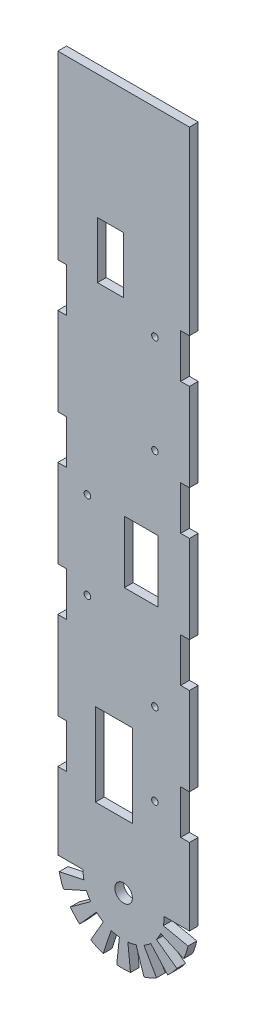
SolidWorks part; units mm, degrees
ref_plane "Front Plane" through (0, 0, 0) normal (0, 0, 1) x (1, 0, 0)
ref_plane "Top Plane" through (0, 0, 0) normal (0, 1, 0) x (1, 0, 0)
ref_plane "Right Plane" through (0, 0, 0) normal (1, 0, 0) x (0, 0, -1)
sketch "Sketch1" plane through (0, 0, 0) normal (0, 0, 1) x (1, 0, 0)
  line L0 (-30, 34.9376) -> (-30, 0)
  line L1 (0, 317.2805) -> (0, 289.6261) construction
  line L2 (30, 317.2805) -> (30, 234.9376)
  line L3 (30, 317.2805) -> (-30, 317.2805)
  line L4 (0, 270.6261) -> (0, 0) construction
  line L5 (-30, 317.2805) -> (30, 317.2805)
  line L6 (18.5, 0) -> (30, 0)
  line L7 (-11.9247, 260.6261) -> (0, 260.6261)
  line L8 (-11.9247, 260.6261) -> (-11.9247, 234.9355)
  line L9 (-11.9247, 234.9355) -> (0, 234.9355)
  line L10 (0, 260.6261) -> (0, 234.9355)
  line L11 (15.5956, 120.6731) -> (0.3306, 120.6731)
  line L12 (15.5956, 120.6731) -> (15.5956, 148.8989)
  line L13 (15.5956, 148.8989) -> (0.3306, 148.8989)
  line L14 (30, 234.9376) -> (26, 234.9355)
  line L15 (26, 234.9355) -> (26, 214.9355)
  line L16 (26, 214.9355) -> (30, 214.9376)
  line L17 (30, 214.9376) -> (30, 174.9376)
  line L18 (26, 174.9355) -> (30, 174.9376)
  line L19 (26, 174.9355) -> (26, 154.9355)
  line L20 (26, 154.9355) -> (30, 154.9376)
  line L21 (30, 154.9376) -> (30, 114.9376)
  line L22 (26, 114.9355) -> (30, 114.9376)
  line L23 (26, 114.9355) -> (26, 94.9355)
  line L24 (26, 94.9355) -> (30, 94.9376)
  line L25 (30, 94.9376) -> (30, 54.9376)
  line L26 (26, 54.9355) -> (30, 54.9376)
  line L27 (26, 54.9355) -> (26, 34.9355)
  line L28 (26, 34.9355) -> (30, 34.9376)
  line L29 (30, 34.9376) -> (30, 0)
  line L30 (-26, 34.9355) -> (-30, 34.9376)
  line L31 (-26, 54.9355) -> (-26, 34.9355)
  line L32 (-26, 54.9355) -> (-30, 54.9376)
  line L33 (-30, 94.9376) -> (-30, 54.9376)
  line L34 (-26, 94.9355) -> (-30, 94.9376)
  line L35 (-26, 114.9355) -> (-26, 94.9355)
  line L36 (-26, 114.9355) -> (-30, 114.9376)
  line L37 (-30, 154.9376) -> (-30, 114.9376)
  line L38 (-26, 154.9355) -> (-30, 154.9376)
  line L39 (-26, 174.9355) -> (-26, 154.9355)
  line L40 (-26, 174.9355) -> (-30, 174.9376)
  line L41 (-30, 214.9376) -> (-30, 174.9376)
  line L42 (-26, 214.9355) -> (-30, 214.9376)
  line L43 (-26, 234.9355) -> (-26, 214.9355)
  line L44 (-30, 234.9376) -> (-26, 234.9355)
  line L45 (-30, 317.2805) -> (-30, 234.9376)
  line L46 (0.3306, 120.6731) -> (0.3306, 148.8989)
  line L47 (-12.8754, 67.1702) -> (4, 67.1702)
  line L48 (-12.8754, 67.1702) -> (-12.8754, 29.4456)
  line L49 (-12.8754, 29.4456) -> (4, 29.4456)
  line L50 (4, 67.1702) -> (4, 29.4456)
  line L51 (18.0957, -3.8464) -> (29.3444, -6.2374)
  line L52 (16.9006, -7.5246) -> (27.4064, -12.2021)
  line L53 (14.9668, -10.874) -> (24.2705, -17.6336)
  line L54 (12.3789, -13.7482) -> (20.0739, -22.2943)
  line L55 (9.25, -16.0215) -> (15, -25.9808)
  line L56 (5.7168, -17.5945) -> (9.2705, -28.5317)
  line L57 (1.9338, -18.3987) -> (3.1359, -29.8357)
  line L58 (-1.9338, -18.3987) -> (-3.1359, -29.8357)
  line L59 (-5.7168, -17.5945) -> (-9.2705, -28.5317)
  line L60 (-9.25, -16.0215) -> (-15, -25.9808)
  line L61 (-12.3789, -13.7482) -> (-20.0739, -22.2943)
  line L62 (-14.9668, -10.874) -> (-24.2705, -17.6336)
  line L63 (-16.9006, -7.5246) -> (-27.4064, -12.2021)
  line L64 (-18.0957, -3.8464) -> (-29.3444, -6.2374)
  line L65 (-18.5, 0) -> (-30, 0)
  arc A0 (-29.3444, -6.2374) -> (-27.4064, -12.2021) centre (0, 0) ccw
  circle A1 centre (14.2729, 226.6267) radius 1.5
  circle A2 centre (0, 0) radius 4
  circle A3 centre (14.2729, 181.7435) radius 1.5
  circle A4 centre (-16.5, 148.8989) radius 1.5
  circle A5 centre (-16.5, 109.236) radius 1.5
  circle A6 centre (14.2729, 80.662) radius 1.5
  circle A7 centre (14.2729, 43.3928) radius 1.5
  arc A8 (-16.9006, -7.5246) -> (-14.9668, -10.874) centre (0, 0) ccw
  arc A9 (18.0957, -3.8464) -> (18.5, 0) centre (0, 0) ccw
  arc A10 (27.4064, -12.2021) -> (29.3444, -6.2374) centre (0, 0) ccw
  arc A11 (-24.2705, -17.6336) -> (-20.0739, -22.2943) centre (0, 0) ccw
  arc A12 (-12.3789, -13.7482) -> (-9.25, -16.0215) centre (0, 0) ccw
  arc A13 (-5.7168, -17.5945) -> (-1.9338, -18.3987) centre (0, 0) ccw
  arc A14 (1.9338, -18.3987) -> (5.7168, -17.5945) centre (0, 0) ccw
  arc A15 (9.25, -16.0215) -> (12.3789, -13.7482) centre (0, 0) ccw
  arc A16 (14.9668, -10.874) -> (16.9006, -7.5246) centre (0, 0) ccw
  arc A17 (20.0739, -22.2943) -> (24.2705, -17.6336) centre (0, 0) ccw
  arc A18 (9.2705, -28.5317) -> (15, -25.9808) centre (0, 0) ccw
  arc A19 (-3.1359, -29.8357) -> (3.1359, -29.8357) centre (0, 0) ccw
  arc A20 (-15, -25.9808) -> (-9.2705, -28.5317) centre (0, 0) ccw
  arc A21 (-18.5, 0) -> (-18.0957, -3.8464) centre (0, 0) ccw
  point P105 (0, 0)
  point P113 (0, 0)
  dimension "D2" = 16
  dimension "D14" = 4
  dimension "D15" = 20
  dimension "D16" = 40
extrude "Boss-Extrude1" add sketch "Sketch1" along normal blind 4
